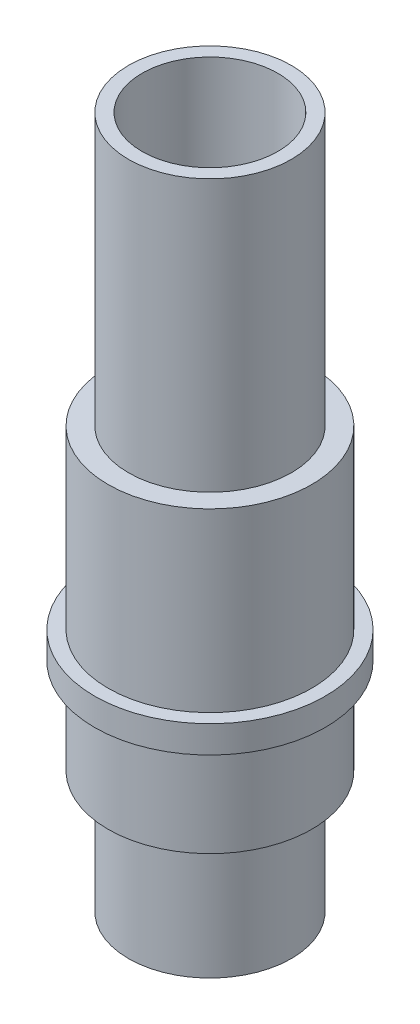
SolidWorks part; units mm, degrees
ref_plane "Plan de face" through (0, 0, 0) normal (0, 0, 1) x (1, 0, 0)
ref_plane "Plan de dessus" through (0, 0, 0) normal (0, 1, 0) x (1, 0, 0)
ref_plane "Plan de droite" through (0, 0, 0) normal (1, 0, 0) x (0, 0, -1)
sketch "Esquisse1" plane through (0, 0, 0) normal (0, 1, 0) x (1, 0, 0)
  circle A0 centre (0, 0) radius 6
  circle A1 centre (0, 0) radius 5
  dimension "D1" = 12
  dimension "D2" = 10
extrude "Boss.-Extru.1" add sketch "Esquisse1" along normal blind 9
sketch "Esquisse2" plane through (0, 9, 0) normal (0, 1, 0) x (1, 0, 0)
  circle A0 centre (0, 0) radius 5
  circle A1 centre (0, 0) radius 7.5
  dimension "D1" = 15
extrude "Boss.-Extru.2" add sketch "Esquisse2" along normal blind 7
sketch "Esquisse3" plane through (0, 16, 0) normal (0, 1, 0) x (1, 0, 0)
  circle A0 centre (0, 0) radius 8.5
  circle A1 centre (0, 0) radius 5
  dimension "D1" = 17
extrude "Boss.-Extru.3" add sketch "Esquisse3" along normal blind 2
sketch "Esquisse4" plane through (0, 18, 0) normal (0, 1, 0) x (1, 0, 0)
  circle A0 centre (0, 0) radius 5
  circle A1 centre (0, 0) radius 7.5
  dimension "D1" = 15
extrude "Boss.-Extru.4" add sketch "Esquisse4" along normal blind 13
sketch "Esquisse5" plane through (0, 31, 0) normal (0, 1, 0) x (1, 0, 0)
  circle A0 centre (0, 0) radius 5
  circle A1 centre (0, 0) radius 6
  dimension "D1" = 12
extrude "Boss.-Extru.5" add sketch "Esquisse5" along normal blind 20
